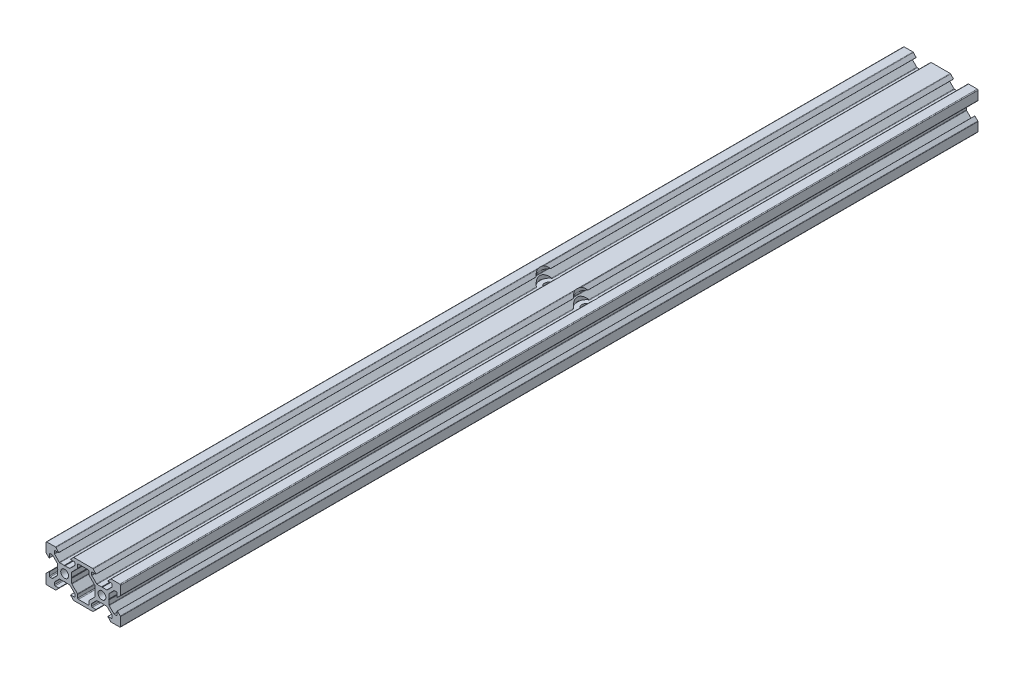
SolidWorks part; units mm, degrees
material "6063-T5"
ref_plane "前视基准面" through (0, 0, 0) normal (0, 0, 1) x (1, 0, 0)
ref_plane "上视基准面" through (0, 0, 0) normal (0, 1, 0) x (1, 0, 0)
ref_plane "右视基准面" through (0, 0, 0) normal (1, 0, 0) x (0, 0, -1)
sketch "草图1" plane through (0, 0, 0) normal (0, 0, 1) x (1, 0, 0)
  line L0 (0, 0) -> (13486.7145, 0) construction
  line L1 (0, 0) -> (0, 13486.7145) construction
  line L2 (0, 0) -> (9536.5473, 9536.5473) construction
  line L3 (0.2, 3.8) -> (2.5737, 3.8)
  line L4 (2.8565, 3.9172) -> (5.3828, 6.4435)
  line L5 (5.5, 6.7263) -> (5.5, 7.8)
  line L6 (5.1, 8.2) -> (3.2, 8.2)
  line L7 (3.1681, 8.2732) -> (4.6563, 9.8725)
  line L8 (4.9492, 10) -> (10, 10)
  line L9 (3.8, 0.2) -> (3.8, 2.5737)
  line L10 (3.9172, 2.8565) -> (6.8753, 5.8146)
  line L11 (10, 5.4182) -> (10, 50005.4182) construction
  line L12 (28.2, -3.2) -> (28.2732, -3.1681)
  line L13 (23.2, -8.2) -> (23.1681, -8.2732)
  line L14 (16.8, -8.2) -> (16.8319, -8.2732)
  line L15 (3.8, -0.2) -> (3.8, -2.5737)
  line L16 (3.9172, -2.8565) -> (6.8753, -5.8146)
  line L17 (28.2, 3.2) -> (28.2732, 3.1681)
  line L18 (16.8, 8.2) -> (16.8319, 8.2732)
  line L19 (23.2, 8.2) -> (23.1681, 8.2732)
  line L20 (20.2, 3.8) -> (22.5737, 3.8)
  line L21 (4.9492, -10) -> (10, -10)
  line L22 (3.1681, -8.2732) -> (4.6563, -9.8725)
  line L23 (5.1, -8.2) -> (3.2, -8.2)
  line L24 (5.5, -6.7263) -> (5.5, -7.8)
  line L25 (2.8565, -3.9172) -> (5.3828, -6.4435)
  line L26 (0.2, -3.8) -> (2.5737, -3.8)
  line L27 (-0.2, -3.8) -> (-2.5737, -3.8)
  line L28 (-2.8565, -3.9172) -> (-5.3828, -6.4435)
  line L29 (-5.5, -6.7263) -> (-5.5, -7.8)
  line L30 (-5.1, -8.2) -> (-3.2, -8.2)
  line L31 (-3.1681, -8.2732) -> (-4.6563, -9.8725)
  line L32 (-4.9492, -10) -> (-9.6, -10)
  line L33 (-10, -4.9492) -> (-10, -9.6)
  line L34 (-8.2732, -3.1681) -> (-9.8725, -4.6563)
  line L35 (-8.2, -5.1) -> (-8.2, -3.2)
  line L36 (-6.7263, -5.5) -> (-7.8, -5.5)
  line L37 (-3.9172, -2.8565) -> (-6.4435, -5.3828)
  line L38 (-3.8, -0.2) -> (-3.8, -2.5737)
  line L39 (-3.8, 0.2) -> (-3.8, 2.5737)
  line L40 (-3.9172, 2.8565) -> (-6.4435, 5.3828)
  line L41 (-6.7263, 5.5) -> (-7.8, 5.5)
  line L42 (-8.2, 5.1) -> (-8.2, 3.2)
  line L43 (-8.2732, 3.1681) -> (-9.8725, 4.6563)
  line L44 (-10, 4.9492) -> (-10, 9.6)
  line L45 (-4.9492, 10) -> (-9.6, 10)
  line L46 (-3.1681, 8.2732) -> (-4.6563, 9.8725)
  line L47 (-5.1, 8.2) -> (-3.2, 8.2)
  line L48 (-5.5, 6.7263) -> (-5.5, 7.8)
  line L49 (-2.8565, 3.9172) -> (-5.3828, 6.4435)
  line L50 (-0.2, 3.8) -> (-2.5737, 3.8)
  line L51 (-3.2, 8.2) -> (-3.1681, 8.2732)
  line L52 (3.2, 8.2) -> (3.1681, 8.2732)
  line L53 (-8.2, 3.2) -> (-8.2732, 3.1681)
  line L54 (22.8565, 3.9172) -> (25.3828, 6.4435)
  line L55 (25.5, 6.7263) -> (25.5, 7.8)
  line L56 (3.2, -8.2) -> (3.1681, -8.2732)
  line L57 (-3.2, -8.2) -> (-3.1681, -8.2732)
  line L58 (-8.2, -3.2) -> (-8.2732, -3.1681)
  line L59 (8.2, -5.1) -> (8.2, -3.2) [skipped]
  line L60 (8.2732, -3.1681) -> (9.8725, -4.6563) [skipped]
  line L61 (6.7263, -5.5) -> (7.8, -5.5) [skipped]
  line L62 (10, -4.9492) -> (10, -9.6) [skipped]
  line L63 (25.1, 8.2) -> (23.2, 8.2)
  line L64 (23.1681, 8.2732) -> (24.6563, 9.8725)
  line L65 (24.9492, 10) -> (29.6, 10)
  line L66 (30, 4.9492) -> (30, 9.6)
  line L67 (28.2732, 3.1681) -> (29.8725, 4.6563)
  line L68 (28.2, 5.1) -> (28.2, 3.2)
  line L69 (26.7263, 5.5) -> (27.8, 5.5)
  line L70 (23.9172, 2.8565) -> (26.4435, 5.3828)
  line L71 (23.8, 0.2) -> (23.8, 2.5737)
  line L72 (23.8, -0.2) -> (23.8, -2.5737)
  line L73 (23.9172, -2.8565) -> (26.4435, -5.3828)
  line L74 (26.7263, -5.5) -> (27.8, -5.5)
  line L75 (28.2, -5.1) -> (28.2, -3.2)
  line L76 (28.2732, -3.1681) -> (29.8725, -4.6563)
  line L77 (30, -4.9492) -> (30, -9.6)
  line L78 (24.9492, -10) -> (29.6, -10)
  line L79 (23.1681, -8.2732) -> (24.6563, -9.8725)
  line L80 (25.1, -8.2) -> (23.2, -8.2)
  line L81 (25.5, -6.7263) -> (25.5, -7.8)
  line L82 (22.8565, -3.9172) -> (25.3828, -6.4435)
  line L83 (20.2, -3.8) -> (22.5737, -3.8)
  line L84 (19.8, -3.8) -> (17.4263, -3.8)
  line L85 (17.1435, -3.9172) -> (14.6172, -6.4435)
  line L86 (14.5, -6.7263) -> (14.5, -7.8)
  line L87 (14.9, -8.2) -> (16.8, -8.2)
  line L88 (16.8319, -8.2732) -> (15.3437, -9.8725)
  line L89 (15.0508, -10) -> (10, -10)
  line L90 (16.0828, -2.8565) -> (13.1247, -5.8146)
  line L91 (16.2, -0.2) -> (16.2, -2.5737)
  line L92 (16.0828, 2.8565) -> (13.1247, 5.8146)
  line L93 (16.2, 0.2) -> (16.2, 2.5737)
  line L94 (15.0508, 10) -> (10, 10)
  line L95 (16.8319, 8.2732) -> (15.3437, 9.8725)
  line L96 (14.9, 8.2) -> (16.8, 8.2)
  line L97 (14.5, 6.7263) -> (14.5, 7.8)
  line L98 (17.1435, 3.9172) -> (14.6172, 6.4435)
  line L99 (19.8, 3.8) -> (17.4263, 3.8)
  line L100 (7, 6.1157) -> (7, 7.7742)
  line L101 (7.4258, 8.2) -> (12.5742, 8.2)
  line L102 (13, 6.1157) -> (13, 7.7742)
  line L103 (13, -6.1157) -> (13, -7.7742)
  line L104 (7.4258, -8.2) -> (12.5742, -8.2)
  line L105 (7, -6.1157) -> (7, -7.7742)
  line L106 (-0.2, 3.8) -> (0, 3.6)
  line L107 (0, 3.6) -> (0.2, 3.8)
  line L108 (3.8, 0.2) -> (3.6, 0)
  line L109 (3.6, 0) -> (3.8, -0.2)
  line L110 (0.2, -3.8) -> (0, -3.6)
  line L111 (0, -3.6) -> (-0.2, -3.8)
  line L112 (-3.8, -0.2) -> (-3.6, 0)
  line L113 (-3.6, 0) -> (-3.8, 0.2)
  line L114 (16.4, 0) -> (16.2, -0.2)
  line L115 (16.2, 0.2) -> (16.4, 0)
  line L116 (20, 3.6) -> (19.8, 3.8)
  line L117 (20.2, 3.8) -> (20, 3.6)
  line L118 (23.6, 0) -> (23.8, 0.2)
  line L119 (23.8, -0.2) -> (23.6, 0)
  line L120 (20, -3.6) -> (20.2, -3.8)
  line L121 (19.8, -3.8) -> (20, -3.6)
  line L122 (20, 0) -> (20, 50000) construction
  arc A0 (-4.9492, 10) -> (-4.6563, 9.8725) centre (-4.9492, 9.6) cw
  arc A1 (-5.1, 8.2) -> (-5.5, 7.8) centre (-5.1, 7.8) ccw
  arc A2 (-5.5, 6.7263) -> (-5.3828, 6.4435) centre (-5.1, 6.7263) ccw
  arc A3 (-2.8565, 3.9172) -> (-2.5737, 3.8) centre (-2.5737, 4.2) ccw
  arc A4 (-10, 9.6) -> (-9.6, 10) centre (-9.6, 9.6) cw
  arc A5 (-9.8725, 4.6563) -> (-10, 4.9492) centre (-9.6, 4.9492) cw
  arc A6 (-7.8, 5.5) -> (-8.2, 5.1) centre (-7.8, 5.1) ccw
  arc A7 (-6.4435, 5.3828) -> (-6.7263, 5.5) centre (-6.7263, 5.1) ccw
  arc A8 (-3.8, 2.5737) -> (-3.9172, 2.8565) centre (-4.2, 2.5737) ccw
  arc A9 (-10, -4.9492) -> (-9.8725, -4.6563) centre (-9.6, -4.9492) cw
  arc A10 (-8.2, -5.1) -> (-7.8, -5.5) centre (-7.8, -5.1) ccw
  arc A11 (-6.7263, -5.5) -> (-6.4435, -5.3828) centre (-6.7263, -5.1) ccw
  arc A12 (-3.9172, -2.8565) -> (-3.8, -2.5737) centre (-4.2, -2.5737) ccw
  arc A13 (-9.6, -10) -> (-10, -9.6) centre (-9.6, -9.6) cw
  arc A14 (-4.6563, -9.8725) -> (-4.9492, -10) centre (-4.9492, -9.6) cw
  arc A15 (-5.5, -7.8) -> (-5.1, -8.2) centre (-5.1, -7.8) ccw
  arc A16 (-5.3828, -6.4435) -> (-5.5, -6.7263) centre (-5.1, -6.7263) ccw
  arc A17 (-2.5737, -3.8) -> (-2.8565, -3.9172) centre (-2.5737, -4.2) ccw
  arc A18 (4.9492, -10) -> (4.6563, -9.8725) centre (4.9492, -9.6) cw
  arc A19 (5.1, -8.2) -> (5.5, -7.8) centre (5.1, -7.8) ccw
  arc A20 (5.5, -6.7263) -> (5.3828, -6.4435) centre (5.1, -6.7263) ccw
  arc A21 (2.8565, -3.9172) -> (2.5737, -3.8) centre (2.5737, -4.2) ccw
  arc A22 (17.4263, 3.8) -> (17.1435, 3.9172) centre (17.4263, 4.2) cw
  arc A23 (14.6172, 6.4435) -> (14.5, 6.7263) centre (14.9, 6.7263) cw
  arc A24 (14.5, 7.8) -> (14.9, 8.2) centre (14.9, 7.8) cw
  arc A25 (15.3437, 9.8725) -> (15.0508, 10) centre (15.0508, 9.6) ccw
  arc A26 (3.8, -2.5737) -> (3.9172, -2.8565) centre (4.2, -2.5737) ccw
  arc A27 (16.2, 2.5737) -> (16.0828, 2.8565) centre (15.8, 2.5737) ccw
  arc A28 (16.2, -2.5737) -> (16.0828, -2.8565) centre (15.8, -2.5737) cw
  arc A29 (17.1435, -3.9172) -> (17.4263, -3.8) centre (17.4263, -4.2) cw
  arc A30 (3.8, 2.5737) -> (3.9172, 2.8565) centre (4.2, 2.5737) cw
  arc A31 (14.5, -6.7263) -> (14.6172, -6.4435) centre (14.9, -6.7263) cw
  arc A32 (4.6563, 9.8725) -> (4.9492, 10) centre (4.9492, 9.6) cw
  arc A33 (5.5, 7.8) -> (5.1, 8.2) centre (5.1, 7.8) ccw
  arc A34 (5.3828, 6.4435) -> (5.5, 6.7263) centre (5.1, 6.7263) ccw
  arc A35 (2.5737, 3.8) -> (2.8565, 3.9172) centre (2.5737, 4.2) ccw
  arc A36 (14.9, -8.2) -> (14.5, -7.8) centre (14.9, -7.8) cw
  arc A37 (15.0508, -10) -> (15.3437, -9.8725) centre (15.0508, -9.6) ccw
  arc A38 (22.5737, -3.8) -> (22.8565, -3.9172) centre (22.5737, -4.2) cw
  arc A39 (25.3828, -6.4435) -> (25.5, -6.7263) centre (25.1, -6.7263) cw
  arc A40 (25.5, -7.8) -> (25.1, -8.2) centre (25.1, -7.8) cw
  arc A41 (24.6563, -9.8725) -> (24.9492, -10) centre (24.9492, -9.6) ccw
  arc A42 (29.6, -10) -> (30, -9.6) centre (29.6, -9.6) ccw
  arc A43 (23.9172, -2.8565) -> (23.8, -2.5737) centre (24.2, -2.5737) cw
  arc A44 (26.7263, -5.5) -> (26.4435, -5.3828) centre (26.7263, -5.1) cw
  arc A45 (28.2, -5.1) -> (27.8, -5.5) centre (27.8, -5.1) cw
  arc A46 (30, -4.9492) -> (29.8725, -4.6563) centre (29.6, -4.9492) ccw
  arc A47 (23.8, 2.5737) -> (23.9172, 2.8565) centre (24.2, 2.5737) cw
  arc A48 (26.4435, 5.3828) -> (26.7263, 5.5) centre (26.7263, 5.1) cw
  arc A49 (27.8, 5.5) -> (28.2, 5.1) centre (27.8, 5.1) cw
  arc A50 (29.8725, 4.6563) -> (30, 4.9492) centre (29.6, 4.9492) ccw
  arc A51 (30, 9.6) -> (29.6, 10) centre (29.6, 9.6) ccw
  arc A52 (22.8565, 3.9172) -> (22.5737, 3.8) centre (22.5737, 4.2) cw
  arc A53 (25.5, 6.7263) -> (25.3828, 6.4435) centre (25.1, 6.7263) cw
  arc A54 (25.1, 8.2) -> (25.5, 7.8) centre (25.1, 7.8) cw
  arc A55 (24.9492, 10) -> (24.6563, 9.8725) centre (24.9492, 9.6) ccw
  arc A56 (13.1247, 5.8146) -> (13, 6.1157) centre (13.4258, 6.1157) cw
  arc A57 (13, 7.7742) -> (12.5742, 8.2) centre (12.5742, 7.7742) ccw
  arc A58 (7, 7.7742) -> (7.4258, 8.2) centre (7.4258, 7.7742) cw
  arc A59 (6.8753, 5.8146) -> (7, 6.1157) centre (6.5742, 6.1157) ccw
  arc A60 (13, -6.1157) -> (13.1247, -5.8146) centre (13.4258, -6.1157) cw
  arc A61 (13, -7.7742) -> (12.5742, -8.2) centre (12.5742, -7.7742) cw
  arc A62 (7.4258, -8.2) -> (7, -7.7742) centre (7.4258, -7.7742) cw
  arc A63 (6.8753, -5.8146) -> (7, -6.1157) centre (6.5742, -6.1157) cw
  circle A64 centre (0, 0) radius 2
  circle A65 centre (20, 0) radius 2
  point P12 (3.1, 8.2)
  point P34 (3.1, -8.2)
  point P41 (-3.1, -8.2)
  point P47 (-8.2, -3.1)
  point P54 (-8.2, 3.1)
  point P60 (-3.1, 8.2)
  point P62 (0, 0)
  point P118 (6.5607, 5.5)
  point P121 (3.8, 2.7393)
  point P124 (10, 10)
  point P127 (4.775, 10)
  point P130 (5.5, 8.2)
  point P133 (5.5, 6.5607)
  point P136 (2.7393, 3.8)
  point P239 (17.2607, 3.8)
  point P240 (14.5, 6.5607)
  point P241 (14.5, 8.2)
  point P242 (15.225, 10)
  point P243 (16.2, 2.7393)
  point P244 (13.4393, 5.5)
  point P245 (20, 0)
  point P246 (23.1, 8.2)
  point P247 (28.2, 3.1)
  point P248 (28.2, -3.1)
  point P249 (23.1, -8.2)
  point P250 (16.9, -8.2)
  point P251 (16.9, 8.2)
  point P253 (10, 8.2)
  point P257 (13, 5.9393)
  point P260 (13, 8.2)
  point P263 (7, 8.2)
  point P266 (7, 5.9393)
  point P269 (13, -5.9393)
  point P272 (13, -8.2)
  point P275 (7, -8.2)
  point P278 (7, -5.9393)
  point P297 (0, 0)
  point P306 (20, 0)
  dimension "D9" = 0.4
  dimension "D13" = 0.4258
  dimension "D14" = 4
  dimension "D3" = 3.1
  dimension "D4" = 1.5
  dimension "D5" = 1.8
  dimension "D6" = 4.775
  dimension "D7" = 20
  dimension "D10" = 10
  dimension "D11" = 10
  dimension "D12" = 1.5
  dimension "D18" = 10
  dimension "D19" = 10
  dimension "D23" = 45
  dimension "D25" = 5.5
  dimension "D26" = 1.8
  dimension "D27" = 1.8
  dimension "D28" = 10
  dimension "D30" = 7.6
  dimension "D31" = 3.8
  dimension "D32" = 3.8
  dimension "D33" = 3.8
  dimension "D34" = 10
  dimension "D35" = 0.4
  dimension "D8" = 4
  dimension "D24" = 4
  dimension "D29" = 4
extrude "凸台-拉伸1" add sketch "草图1" along normal blind 460
hole_wizard "Ø5.0 (5) 直径孔1" positions "草图9" profile "草图10" hole size "Ø5.0" standard "GB" end condition through all
sketch "草图9" plane through (0, 10, 0) normal (0, 1, 0) x (1, 0, 0)
  line L0 (20, -460) -> (20, 0) construction
  line L1 (0, -460) -> (0, 0) construction
  line L2 (-4.9492, 0) -> (-9.6, 0) construction
  point P0 (20, -200)
  point P2 (0, -200)
  dimension "D1" = 200
sketch "草图10" plane through (20, 10, 200) normal (1, 0, 0) x (0, 0, 1)
  line L0 (0, 0) -> (0, 20)
  line L1 (0, 20) -> (2.5, 20)
  line L2 (2.5, 20) -> (2.5, 0)
  line L5 (2.5, 0) -> (0, 0)
  line L11 (0, -6.35) -> (0, 107.95) construction
  dimension "通孔孔直径" = 5
  dimension "通孔孔深度" = 20
hole_wizard "Ø10.0 (10) 直径孔1" positions "草图11" profile "草图12" hole size "Ø10.0" standard "GB"
sketch "草图11" plane through (0, 10, 0) normal (0, 1, 0) x (1, 0, 0)
  point P0 (20, -200)
  point P3 (0, -200)
sketch "草图12" plane through (20, 10, 200) normal (1, 0, 0) x (0, 0, 1)
  line L0 (0, 0) -> (0, 6.2)
  line L1 (0, 6.2) -> (5, 6.2)
  line L2 (5, 6.2) -> (5, 0)
  line L5 (5, 0) -> (0, 0)
  line L10 (0, 6.2) -> (-5, 6.2) construction
  line L11 (0, -6.35) -> (0, 107.95) construction
  dimension "孔直径" = 10
  dimension "孔深度" = 6.2
  dimension "导头角度" = 180
hole_wizard "M5 螺纹孔1" positions "草图5" profile "草图4" tap size "M5" standard "GB"
sketch "草图5" plane through (0, 0, 0) normal (0, 0, -1) x (-1, 0, 0)
  point P0 (0, 0)
  point P3 (-20, 0)
sketch "草图4" plane through (0, 0, 0) normal (1, 0, 0) x (0, 1, 0)
  line L0 (0, 0) -> (0, 16.2618)
  line L1 (0, 16.2618) -> (2.1, 15)
  line L2 (2.1, 15) -> (2.1, 0)
  line L5 (2.1, 0) -> (0, 0)
  line L10 (0, 16.2618) -> (-2.1, 15) construction
  line L11 (0, -6.35) -> (0, 107.95) construction
  dimension "螺纹孔钻头直径" = 4.2
  dimension "螺纹孔钻头深度" = 15
  dimension "导头角度" = 118
cosmetic thread "孔螺蚊线1" parameters "D1"=15, "D2"=5
cosmetic thread "孔螺蚊线2" parameters "D1"=15, "D2"=5
hole_wizard "M5 螺纹孔2" positions "草图8" profile "草图7" tap size "M5" standard "GB"
sketch "草图8" plane through (0, 0, 460) normal (0, 0, 1) x (1, 0, 0)
  point P0 (0, 0)
  point P3 (20, 0)
sketch "草图7" plane through (0, 0, 460) normal (1, 0, 0) x (0, -1, 0)
  line L0 (0, 0) -> (0, 16.2618)
  line L1 (0, 16.2618) -> (2.1, 15)
  line L2 (2.1, 15) -> (2.1, 0)
  line L5 (2.1, 0) -> (0, 0)
  line L10 (0, 16.2618) -> (-2.1, 15) construction
  line L11 (0, -6.35) -> (0, 107.95) construction
  dimension "螺纹孔钻头直径" = 4.2
  dimension "螺纹孔钻头深度" = 15
  dimension "导头角度" = 118
cosmetic thread "孔螺蚊线3" parameters "D1"=15, "D2"=5
cosmetic thread "孔螺蚊线4" parameters "D1"=15, "D2"=5
hole_wizard "M4 螺纹孔1" [suppressed] positions "草图13" profile "草图14" tap size "M4" standard "GB"
sketch "草图13" plane through (0, 3.8, 0) normal (0, 1, 0) x (1, 0, 0)
  line L0 (0, -197.5) -> (0, 0) construction
  line L1 (20, -197.5) -> (20, 0) construction
  line L2 (29.6, 0) -> (24.9492, 0) construction
  line L3 (0, -460) -> (0, -202.5) construction
  line L4 (20, -460) -> (20, -202.5) construction
  line L5 (29.6, -460) -> (24.9492, -460) construction
  point P0 (0, -390)
  point P2 (20, -390)
  point P4 (0, -25)
  point P6 (20, -25)
  dimension "D1" = 25
  dimension "D2" = 70
sketch "草图14" plane through (0, 3.8, 390) normal (1, 0, 0) x (0, 0, 1)
  line L0 (0, 0) -> (0, 13.8)
  line L1 (0, 13.8) -> (1.65, 13.8)
  line L2 (1.65, 13.8) -> (1.65, 0)
  line L5 (1.65, 0) -> (0, 0)
  line L11 (0, -6.35) -> (0, 107.95) construction
  dimension "通孔螺纹孔钻头直径" = 3.3
  dimension "通孔螺纹孔钻头深度" = 13.8
cosmetic thread "孔螺蚊线14" [suppressed] parameters "D2"=4
cosmetic thread "孔螺蚊线15" [suppressed] parameters "D2"=4
cosmetic thread "孔螺蚊线16" [suppressed] parameters "D2"=4
cosmetic thread "孔螺蚊线17" [suppressed] parameters "D2"=4
